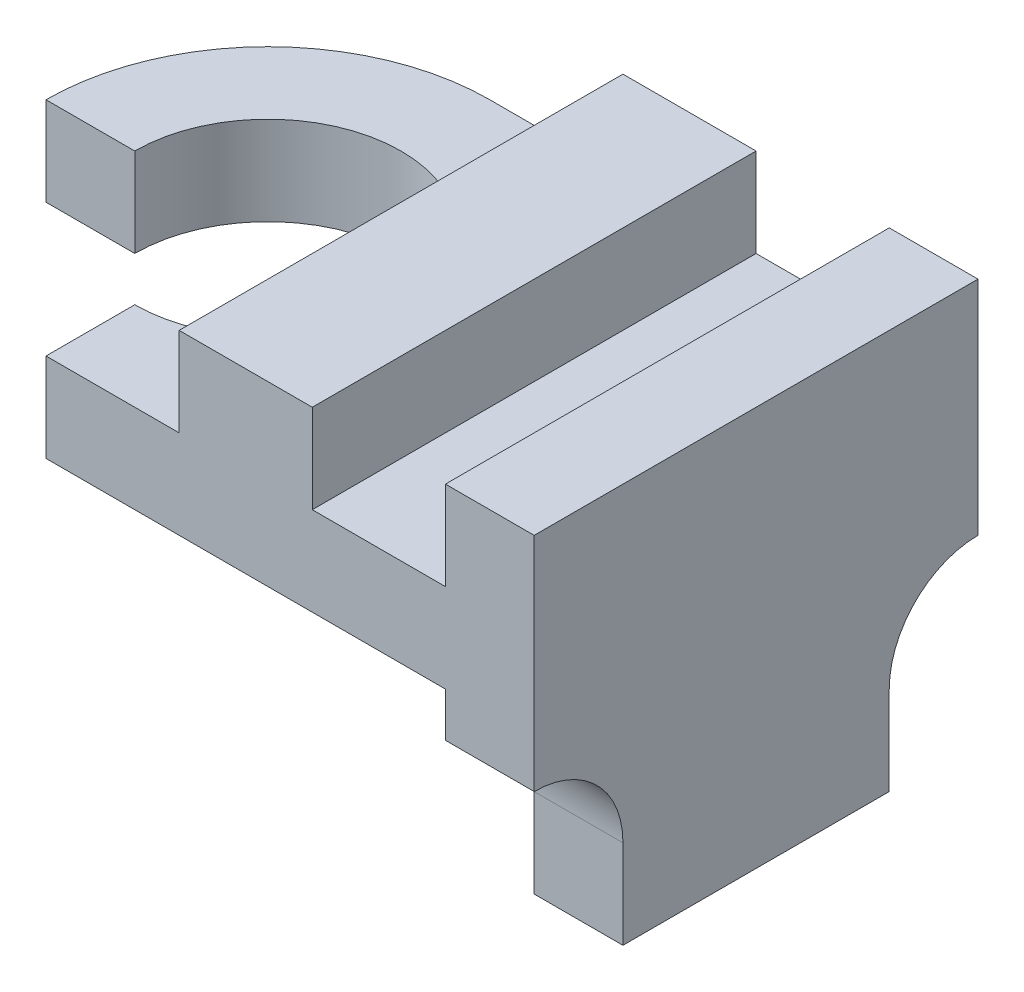
SolidWorks part; units mm, degrees
ref_plane "Front Plane" through (0, 0, 0) normal (0, 0, 1) x (1, 0, 0)
ref_plane "Top Plane" through (0, 0, 0) normal (0, 1, 0) x (1, 0, 0)
ref_plane "Right Plane" through (0, 0, 0) normal (1, 0, 0) x (0, 0, -1)
sketch "Sketch2" plane through (0, 0, 0) normal (0, 0, 1) x (1, 0, 0)
  line L1 (0, 0) -> (110, 0)
  line L2 (0, 0) -> (0, 40)
  line L3 (0, 40) -> (110, 40)
  line L4 (110, 0) -> (110, 40)
  dimension "D1" = 110
  dimension "D2" = 40
extrude "Boss-Extrude1" add sketch "Sketch2" along normal blind 100
sketch "Sketch3" plane through (0, 0, 100) normal (0, 0, 1) x (1, 0, 0)
  line L0 (110, 40) -> (0, 40) construction
  line L1 (90, 40) -> (60, 40)
  line L2 (90, 40) -> (90, 20)
  line L3 (90, 20) -> (60, 20)
  line L4 (60, 40) -> (60, 20)
  line L6 (0, 40) -> (30, 40)
  line L7 (0, 40) -> (0, 20)
  line L8 (0, 20) -> (30, 20)
  line L9 (30, 40) -> (30, 20)
  dimension "D1" = 30
  dimension "D2" = 30
  dimension "D3" = 20
  dimension "D4" = 20
  dimension "D5" = 20
extrude "Cut-Extrude1" cut sketch "Sketch3" against normal blind 100
sketch "Sketch4" plane through (0, 0, 0) normal (0, -1, 0) x (-1, 0, 0)
  line L0 (0, 0) -> (-110, 0) construction
  line L1 (-110, -100) -> (-90, -100)
  line L2 (-110, -100) -> (-110, 0)
  line L3 (-110, 0) -> (-90, 0)
  line L4 (-90, -100) -> (-90, 0)
  dimension "D1" = 0
  dimension "D2" = 20
extrude "Boss-Extrude3" add sketch "Sketch4" along normal blind 50
sketch "Sketch6" plane through (90, 0, 0) normal (-1, 0, 0) x (0, 0, 1)
  line L0 (100, -50) -> (100, 0) construction
  line L1 (80, -30) -> (80, -50)
  line L2 (100, -50) -> (0, -50) construction
  line L3 (100, -10) -> (100, -50)
  line L4 (100, -50) -> (80, -50)
  line L5 (0, -50) -> (0, 0) construction
  line L6 (20, -30) -> (20, -50)
  line L7 (20, -50) -> (0, -50)
  line L8 (0, -50) -> (0, -10)
  arc A0 (100, -10) -> (80, -30) centre (100, -30) ccw
  arc A1 (0, -10) -> (20, -30) centre (0, -30) cw
  dimension "D1" = 20
  dimension "D5" = 20
  dimension "D2" = 10
  dimension "D3" = 20
  dimension "D4" = 10
  dimension "D6" = 20
  dimension "D7" = 20
extrude "Cut-Extrude2" cut sketch "Sketch6" against normal blind 50
sketch "Sketch7" plane through (0, 0, 0) normal (0, -1, 0) x (-1, 0, 0)
  line L0 (-90, -100) -> (-90, 0) construction
  line L1 (-90, -60) -> (-50, -60)
  line L2 (-90, -60) -> (-90, -40)
  line L3 (-90, -40) -> (-50, -40)
  line L4 (-50, -60) -> (-50, -40)
  line L5 (0, -100) -> (-90, -100) construction
  dimension "D1" = 40
  dimension "D2" = 20
  dimension "D3" = 40
  dimension "D4" = 40
extrude "Boss-Extrude4" add sketch "Sketch7" along normal blind 30
sketch "Sketch8" plane through (0, 0, 60) normal (0, 0, 1) x (1, 0, 0)
  line L0 (90, -30) -> (50, 0)
  line L1 (50, 0) -> (50, -30)
  line L2 (50, -30) -> (90, -30)
extrude "Cut-Extrude3" cut sketch "Sketch8" against normal blind 30
sketch "Sketch9" plane through (0, 0, 0) normal (0, -1, 0) x (-1, 0, 0)
  line L1 (0, 0) -> (50, 0)
  line L2 (0, 0) -> (0, -50)
  line L3 (0, -50) -> (50, -50)
  line L4 (50, 0) -> (50, -50)
  dimension "D1" = 50
  dimension "D2" = 50
extrude "Boss-Extrude5" add sketch "Sketch9" against normal blind 20
sketch "Sketch10" plane through (0, 0, 0) normal (0, -1, 0) x (-1, 0, 0)
  line L0 (0, -50) -> (50, -50) construction
  line L1 (0, -100) -> (0, -50) construction
  line L2 (30, -50) -> (0, -50)
  line L3 (0, -50) -> (0, -80)
  arc A0 (0, -80) -> (30, -50) centre (0, -50) cw
  dimension "D1" = 30
  dimension "D2" = 20
  dimension "D3" = 0
  dimension "D4" = 20
extrude "Cut-Extrude5" cut sketch "Sketch10" against normal blind 20
sketch "Sketch12" plane through (0, 0, 0) normal (0, -1, 0) x (-1, 0, 0)
  line L0 (50, 0) -> (-90, 0) construction
  line L1 (50, -50) -> (50, 0)
  line L2 (50, 0) -> (0, 0)
  arc A0 (50, -50) -> (0, 0) centre (0, -50) ccw
extrude "Cut-Extrude6" cut sketch "Sketch12" against normal blind 20
